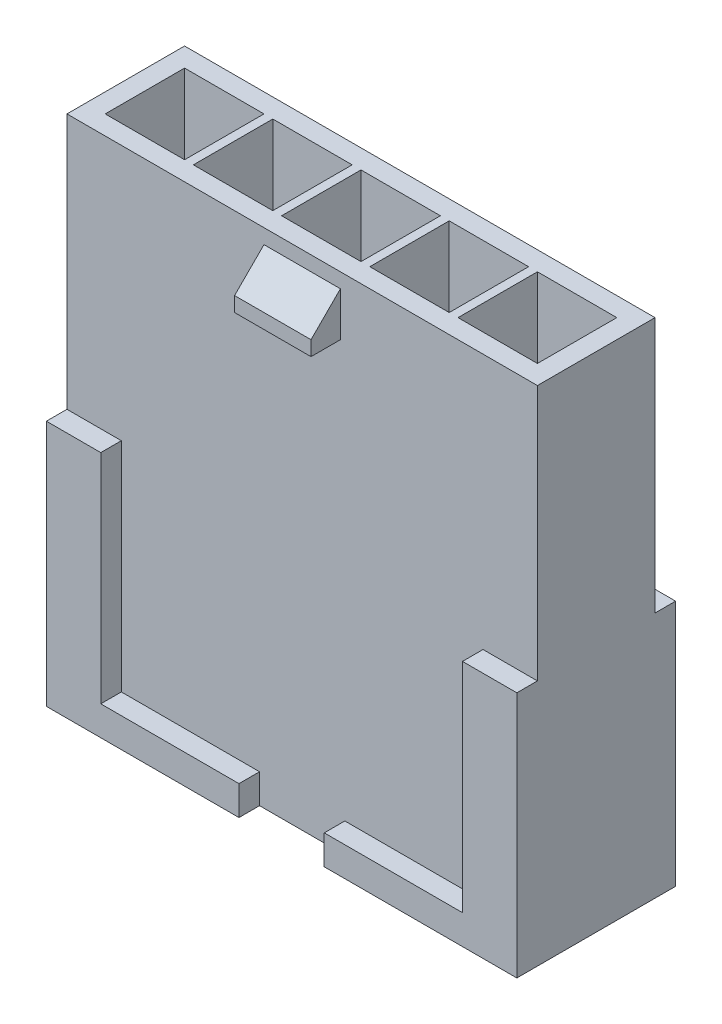
SolidWorks part; units mm, degrees
ref_plane "Front Plane" through (0, 0, 0) normal (0, 0, 1) x (1, 0, 0)
ref_plane "Top Plane" through (0, 0, 0) normal (0, 1, 0) x (1, 0, 0)
ref_plane "Right Plane" through (0, 0, 0) normal (1, 0, 0) x (0, 0, -1)
sketch "Sketch1" plane through (0, 0, 0) normal (0, 1, 0) x (1, 0, 0)
  line L0 (1.65, 1.35) -> (4.35, 1.35)
  line L1 (-8, 2) -> (8, 2)
  line L2 (-8, 2) -> (-8, -2)
  line L3 (-8, -2) -> (8, -2)
  line L4 (8, 2) -> (8, -2)
  line L5 (-8, 2) -> (8, -2) construction
  line L6 (-8, -2) -> (8, 2) construction
  line L7 (-1.35, 1.35) -> (1.35, 1.35)
  line L8 (-1.35, 1.35) -> (-1.35, -1.35)
  line L9 (-1.35, -1.35) -> (1.35, -1.35)
  line L10 (1.35, 1.35) -> (1.35, -1.35)
  line L11 (-1.35, 1.35) -> (1.35, -1.35) construction
  line L12 (-1.35, -1.35) -> (1.35, 1.35) construction
  line L13 (4.35, 1.35) -> (4.35, -1.35)
  line L14 (1.65, -1.35) -> (4.35, -1.35)
  line L15 (1.65, 1.35) -> (1.65, -1.35)
  line L16 (4.65, 1.35) -> (7.35, 1.35)
  line L17 (7.35, 1.35) -> (7.35, -1.35)
  line L18 (4.65, -1.35) -> (7.35, -1.35)
  line L19 (4.65, 1.35) -> (4.65, -1.35)
  line L20 (0, 2) -> (0, -2) construction
  line L21 (-4.65, 1.35) -> (-4.65, -1.35)
  line L22 (-4.65, 1.35) -> (-7.35, 1.35)
  line L23 (-7.35, 1.35) -> (-7.35, -1.35)
  line L24 (-4.65, -1.35) -> (-7.35, -1.35)
  line L25 (-1.65, 1.35) -> (-1.65, -1.35)
  line L26 (-1.65, 1.35) -> (-4.35, 1.35)
  line L27 (-4.35, 1.35) -> (-4.35, -1.35)
  line L28 (-1.65, -1.35) -> (-4.35, -1.35)
  point P0 (0, 0)
  point P6 (0, 0)
  dimension "D1" = 4
  dimension "D2" = 16
  dimension "D3" = 2.7
  dimension "D5" = 3
  dimension "D4" = 3
extrude "Boss-Extrude1" add sketch "Sketch1" along normal blind 17.1
sketch "Sketch2" plane through (0, 0, 2) normal (0, 0, 1) x (1, 0, 0)
  line L0 (0, 17.1) -> (0, 0) construction
  line L1 (-8, 17.1) -> (8, 17.1) construction
  line L2 (-8, 17.1) -> (-8, 0) construction
  line L3 (-8, 8.4) -> (-6.15, 8.4)
  line L4 (-8, 8.4) -> (-8, 0)
  line L5 (-8, 0) -> (-6.15, 0)
  line L6 (-6.15, 8.4) -> (-6.15, 0)
  line L7 (-8, 0) -> (8, 0) construction
  line L8 (1.45, 1) -> (1.45, 0)
  line L9 (-6.15, 1) -> (-1.45, 1)
  line L10 (-6.15, 1) -> (-6.15, 0)
  line L11 (-6.15, 0) -> (-1.45, 0)
  line L12 (-1.45, 1) -> (-1.45, 0)
  line L13 (6.15, 1) -> (1.45, 1)
  line L14 (8, 0) -> (6.15, 0)
  line L15 (8, 8.4) -> (8, 0)
  line L16 (8, 8.4) -> (6.15, 8.4)
  line L17 (6.15, 8.4) -> (6.15, 0)
  line M10 (-8, 0) -> (8, 0)
  line M11 (8, 0) -> (8, 17.1)
  line M13 (-8, 17.1) -> (-8, 0)
  dimension "D1" = 8.4
  dimension "D2" = 1.85
  dimension "D3" = 1
  dimension "D4" = 2.9
extrude "Boss-Extrude2" add sketch "Sketch2" along normal blind 0.7 contours L6 L3 M13 M10 | L12 L9 L6 M10 | L17 L13 L8 M10 | L16 L17 M10 M11
sketch "Sketch3" plane through (0, 0, 0) normal (1, 0, 0) x (0, 0, -1)
  line L0 (-2, 16.6) -> (-3, 15.6)
  line L1 (-2, 17.1) -> (-2, 8.4) construction
  line L2 (-3, 15.6) -> (-3, 15.1)
  line L3 (-3, 15.1) -> (-2, 15.1)
  line L4 (-2, 15.1) -> (-2, 16.6)
  line L5 (-2, 17.1) -> (2, 17.1) construction
  dimension "D1" = 0.5
  dimension "D2" = 1
  dimension "D3" = 0.5
  dimension "D4" = 45
extrude "Boss-Extrude3" add sketch "Sketch3" along normal mid plane 2.6
sketch "Sketch4" plane through (0, 0, -2) normal (0, 0, -1) x (-1, 0, 0)
  line L0 (6.15, 1) -> (6.15, 8.4) construction
  line L1 (6.15, 8.4) -> (8, 8.4) construction
  line L2 (8, 8.4) -> (8, 0) construction
  line L3 (8, 0) -> (1.45, 0) construction
  line L4 (1.45, 0) -> (1.45, 1) construction
  line L5 (1.45, 1) -> (6.15, 1) construction
  line L6 (-1.45, 0) -> (-8, 0) construction
  line L7 (-8, 0) -> (-8, 8.4) construction
  line L8 (-8, 8.4) -> (-6.15, 8.4) construction
  line L9 (-6.15, 8.4) -> (-6.15, 1) construction
  line L10 (-6.15, 1) -> (-1.45, 1) construction
  line L11 (-1.45, 1) -> (-1.45, 0) construction
  line L12 (6.15, 1) -> (6.15, 8.4)
  line L13 (6.15, 8.4) -> (8, 8.4)
  line L14 (8, 8.4) -> (8, 0)
  line L15 (8, 0) -> (1.45, 0)
  line L16 (1.45, 0) -> (1.45, 1)
  line L17 (1.45, 1) -> (6.15, 1)
  line L18 (-1.45, 0) -> (-8, 0)
  line L19 (-8, 0) -> (-8, 8.4)
  line L20 (-8, 8.4) -> (-6.15, 8.4)
  line L21 (-6.15, 8.4) -> (-6.15, 1)
  line L22 (-6.15, 1) -> (-1.45, 1)
  line L23 (-1.45, 1) -> (-1.45, 0)
  line L25 (-1.45, 1) -> (1.45, 1)
  line L26 (-1.45, 1) -> (-1.45, 0)
  line L27 (-1.45, 0) -> (1.45, 0)
  line L28 (1.45, 1) -> (1.45, 0)
  line M1 (-8, 0) -> (8, 0)
  line M2 (8, 0) -> (8, 17.1)
  line M4 (-8, 17.1) -> (-8, 0)
extrude "Boss-Extrude4" add sketch "Sketch4" along normal blind 0.7 contours L23 L22 L21 L20 M4 M1 | L25 L23 L16 M1 | L17 L16 L13 L12 M1 M2
